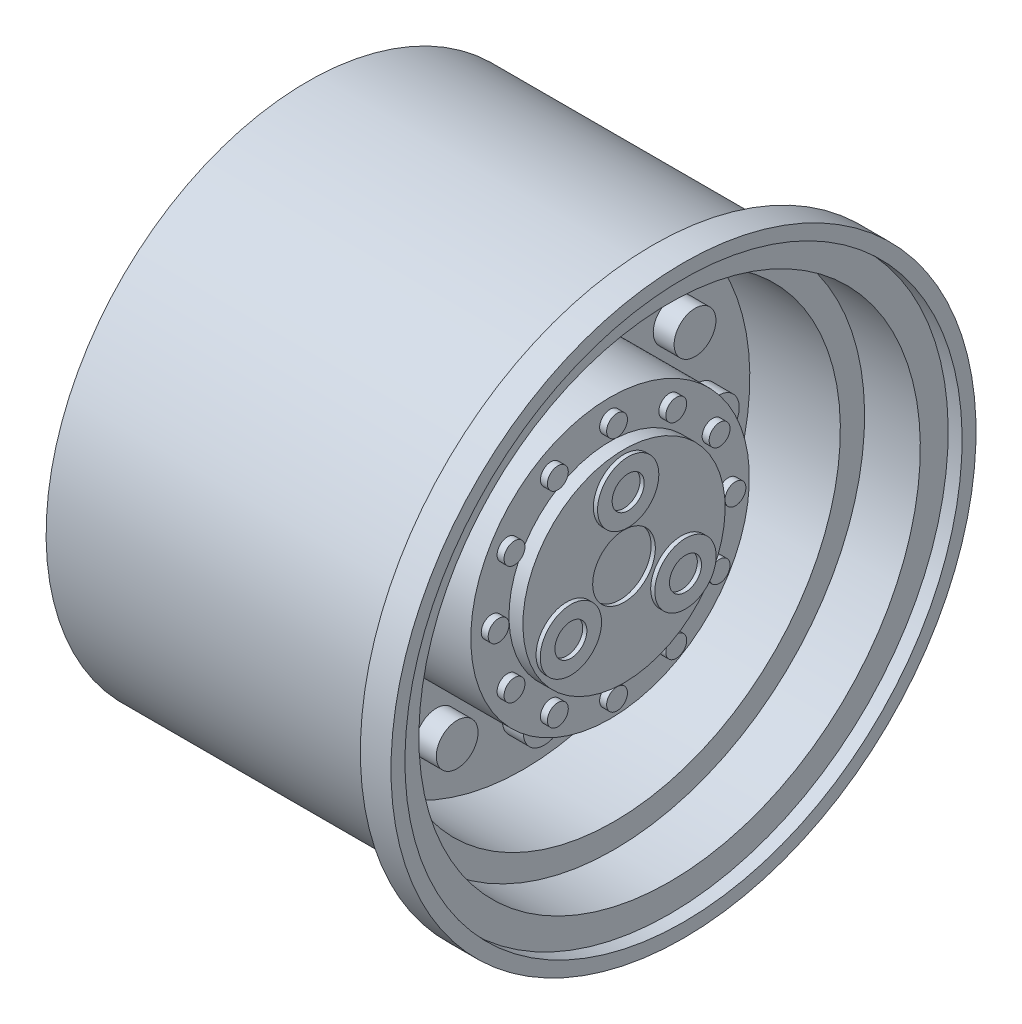
SolidWorks part; units mm, degrees
ref_plane "Front Plane" through (0, 0, 0) normal (0, 0, 1) x (1, 0, 0)
ref_plane "Top Plane" through (0, 0, 0) normal (0, 1, 0) x (1, 0, 0)
ref_plane "Right Plane" through (0, 0, 0) normal (1, 0, 0) x (0, 0, -1)
sketch "Sketch1" plane through (0, 0, 0) normal (0, 0, 1) x (1, 0, 0)
  line L0 (-22.785, 0) -> (22.785, 0)
  line L1 (-22.785, 0) -> (-22.785, 16.25)
  line L2 (-22.785, 16.25) -> (-19.035, 16.25)
  line L3 (-19.035, 16.25) -> (-19.035, 22.5)
  line L4 (-19.035, 22.5) -> (-14.535, 22.5)
  line L5 (-14.535, 22.5) -> (-14.535, 40.65)
  line L6 (-14.535, 40.65) -> (-26.535, 40.65)
  line L7 (-26.535, 40.65) -> (-26.535, 42.5)
  line L8 (-26.535, 42.5) -> (-34.035, 42.5)
  line L9 (-34.035, 42.5) -> (-34.035, 46.9)
  line L10 (-34.035, 46.9) -> (27.965, 46.9)
  line L11 (27.965, 46.9) -> (27.965, 52.5)
  line L12 (27.965, 52.5) -> (33.465, 52.5)
  line L13 (33.465, 52.5) -> (33.465, 50)
  line L14 (33.465, 50) -> (30.965, 50)
  line L15 (30.965, 50) -> (30.965, 45)
  line L16 (30.965, 45) -> (20.965, 45)
  line L17 (20.965, 45) -> (20.965, 40.65)
  line L18 (20.965, 40.65) -> (4.715, 40.65)
  line L19 (4.715, 40.65) -> (4.715, 25)
  line L20 (4.715, 25) -> (20.285, 25)
  line L21 (20.285, 25) -> (20.285, 18.15)
  line L22 (20.285, 18.15) -> (22.785, 18.15)
  line L23 (22.785, 18.15) -> (22.785, 0)
  line L24 (0, 0) -> (0, 80.9627) construction
  point P4 (0, 0)
  point P19 (23.0614, 14.5555)
  point P32 (33.465, 51.25)
  dimension "D1" = 16.25
  dimension "D2" = 22.5
  dimension "D3" = 40.65
  dimension "D4" = 42.5
  dimension "D5" = 46.9
  dimension "D6" = 19.5
  dimension "D7" = 7.5
  dimension "D8" = 11.25
  dimension "D9" = 15
  dimension "D10" = 67.5
  dimension "D11" = 2.5
  dimension "D12" = 5.5
  dimension "D13" = 12.5
  dimension "D14" = 28.75
  dimension "D15" = 2.5
  dimension "D16" = 52.5
  dimension "D17" = 50
  dimension "D18" = 45
  dimension "D19" = 40.65
  dimension "D20" = 18.15
  dimension "D21" = 25
  dimension "D22" = 4.715
revolve "Revolve1" add sketch "Sketch1" angle 360 about L0
sketch "Sketch2" plane through (4.715, 0, 0) normal (1, 0, 0) x (0, 0, -1)
  circle A0 centre (0, 0) radius 31.25 construction
  circle A1 centre (0, 31.25) radius 3.75
  circle A2 centre (15.625, 27.0633) radius 3.75
  circle A3 centre (27.0633, 15.625) radius 3.75
  circle A4 centre (31.25, 0) radius 3.75
  circle A5 centre (27.0633, -15.625) radius 3.75
  circle A6 centre (15.625, -27.0633) radius 3.75
  circle A7 centre (0, -31.25) radius 3.75
  circle A8 centre (-15.625, -27.0633) radius 3.75
  circle A9 centre (-27.0633, -15.625) radius 3.75
  circle A10 centre (-31.25, 0) radius 3.75
  circle A11 centre (-27.0633, 15.625) radius 3.75
  circle A12 centre (-15.625, 27.0633) radius 3.75
  point P30 (0, 0)
  dimension "D1" = 62.5
  dimension "D2" = 7.5
  dimension "D3" = 12
extrude "Boss-Extrude1" add sketch "Sketch2" along normal blind 3.75
sketch "Sketch3" plane through (20.285, 0, 0) normal (1, 0, 0) x (0, 0, -1)
  circle A0 centre (0, 0) radius 21.25 construction
  circle A1 centre (0, 21.25) radius 1.875
  circle A2 centre (10.625, 18.403) radius 1.875
  circle A3 centre (18.403, 10.625) radius 1.875
  circle A4 centre (21.25, 0) radius 1.875
  circle A5 centre (18.403, -10.625) radius 1.875
  circle A6 centre (10.625, -18.403) radius 1.875
  circle A7 centre (0, -21.25) radius 1.875
  circle A8 centre (-10.625, -18.403) radius 1.875
  circle A9 centre (-18.403, -10.625) radius 1.875
  circle A10 centre (-21.25, 0) radius 1.875
  circle A11 centre (-18.403, 10.625) radius 1.875
  circle A12 centre (-10.625, 18.403) radius 1.875
  point P29 (0, 0)
  dimension "D1" = 42.5
  dimension "D2" = 3.75
  dimension "D3" = 12
extrude "Boss-Extrude2" add sketch "Sketch3" along normal blind 1.25
sketch "Sketch4" plane through (22.785, 0, 0) normal (1, 0, 0) x (0, 0, -1)
  circle A0 centre (0, 0) radius 5.625
  dimension "D1" = 11.25
extrude "Cut-Extrude1" cut sketch "Sketch4" against normal blind 0.75
sketch "Sketch5" plane through (22.785, 0, 0) normal (1, 0, 0) x (0, 0, -1)
  circle A0 centre (0, 0) radius 11.875 construction
  circle A1 centre (0, 11.875) radius 5.5
  circle A2 centre (0, 11.875) radius 2.875
  circle A3 centre (10.2841, -5.9375) radius 2.875
  circle A4 centre (10.2841, -5.9375) radius 5.5
  circle A5 centre (0, 0) radius 11.875 construction
  circle A6 centre (-10.2841, -5.9375) radius 2.875
  circle A7 centre (-10.2841, -5.9375) radius 5.5
  circle A8 centre (0, 0) radius 11.875 construction
  point P16 (0, 0)
  dimension "D1" = 23.75
  dimension "D2" = 11
  dimension "D3" = 5.75
  dimension "D4" = 3
extrude "Boss-Extrude3" add sketch "Sketch5" along normal blind 0.75
sketch "Sketch7" plane through (-19.035, 0, 0) normal (-1, 0, 0) x (0, 0, 1)
  circle A0 centre (0, 0) radius 19.05 construction
  circle A1 centre (0, 19.05) radius 1.875
  circle A2 centre (0, 0) radius 19.05 construction
  circle A3 centre (9.525, 16.4978) radius 1.875
  circle A4 centre (0, 0) radius 19.05 construction
  circle A5 centre (16.4978, 9.525) radius 1.875
  circle A6 centre (0, 0) radius 19.05 construction
  circle A7 centre (19.05, 0) radius 1.875
  circle A8 centre (0, 0) radius 19.05 construction
  circle A9 centre (16.4978, -9.525) radius 1.875
  circle A10 centre (0, 0) radius 19.05 construction
  circle A11 centre (9.525, -16.4978) radius 1.875
  circle A12 centre (0, 0) radius 19.05 construction
  circle A13 centre (0, -19.05) radius 1.875
  circle A14 centre (0, 0) radius 19.05 construction
  circle A15 centre (-9.525, -16.4978) radius 1.875
  circle A16 centre (0, 0) radius 19.05 construction
  circle A17 centre (-16.4978, -9.525) radius 1.875
  circle A18 centre (0, 0) radius 19.05 construction
  circle A19 centre (-19.05, 0) radius 1.875
  circle A20 centre (0, 0) radius 19.05 construction
  circle A21 centre (-16.4978, 9.525) radius 1.875
  circle A22 centre (0, 0) radius 19.05 construction
  circle A23 centre (-9.525, 16.4978) radius 1.875
  point P40 (0, 0)
  dimension "D1" = 38.1
  dimension "D2" = 3.75
  dimension "D3" = 12
extrude "Boss-Extrude4" add sketch "Sketch7" along normal blind 1.25
sketch "Sketch8" plane through (-22.785, 0, 0) normal (-1, 0, 0) x (0, 0, 1)
  circle A0 centre (0, 0) radius 6.25
  dimension "D1" = 12.5
extrude "Cut-Extrude2" cut sketch "Sketch8" against normal blind 25
